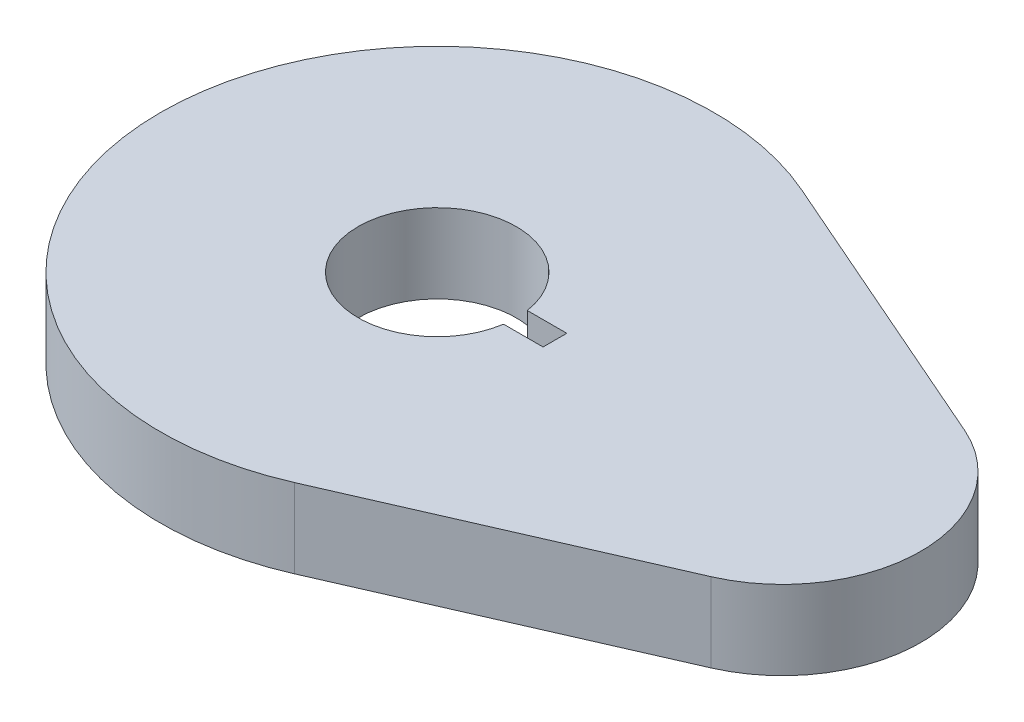
SolidWorks part; units mm, degrees
ref_plane "Front" through (0, 0, 0) normal (0, 0, 1) x (1, 0, 0)
ref_plane "Top" through (0, 0, 0) normal (0, 1, 0) x (1, 0, 0)
ref_plane "Right" through (0, 0, 0) normal (1, 0, 0) x (0, 0, -1)
sketch "Sketch1" plane through (0, 0, 0) normal (0, 1, 0) x (1, 0, 0)
  line L0 (14.0287, -32.0655) -> (50.675, -16.0328)
  line L1 (50.675, 16.0328) -> (14.0287, 32.0655)
  line L2 (14.8869, 1.5) -> (14.8869, -1.5)
  line L3 (9.8869, -1.5) -> (14.8869, -1.5)
  line L4 (9.8869, 1.5) -> (14.8869, 1.5)
  arc A0 (14.0287, 32.0655) -> (14.0287, -32.0655) centre (0, 0) ccw
  arc A1 (50.675, 16.0328) -> (50.675, -16.0328) centre (43.6606, 0) cw
  circle A2 centre (0, 0) radius 10
  point P13 (14.8869, 0)
  dimension "D1" = 35
  dimension "D2" = 17.5
  dimension "D5" = 20
  dimension "D3" = 40
  dimension "D4" = 5
  dimension "D6" = 3
extrude "Boss-Extrude1" add sketch "Sketch1" along normal blind 10 contours A1 L1 A0 L0 A2 L4 L2 L3
